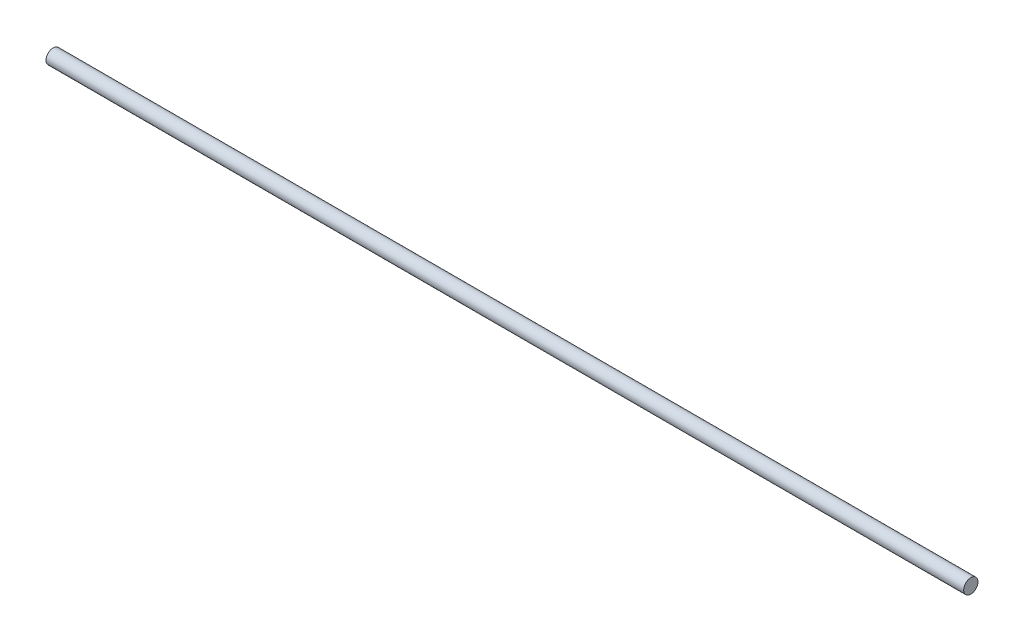
SolidWorks part; units mm, degrees
material "6061-T6 (SS)"
ref_plane "Front Plane" through (0, 0, 0) normal (0, 0, 1) x (1, 0, 0)
ref_plane "Top Plane" through (0, 0, 0) normal (0, 1, 0) x (1, 0, 0)
ref_plane "Right Plane" through (0, 0, 0) normal (1, 0, 0) x (0, 0, -1)
sketch "Sketch1" plane through (0, 0, 0) normal (1, 0, 0) x (0, 0, -1)
  circle A0 centre (0, 0) radius 4.7625
  dimension "D1" = 9.525
extrude "Boss-Extrude1" add sketch "Sketch1" along normal blind 609.6
